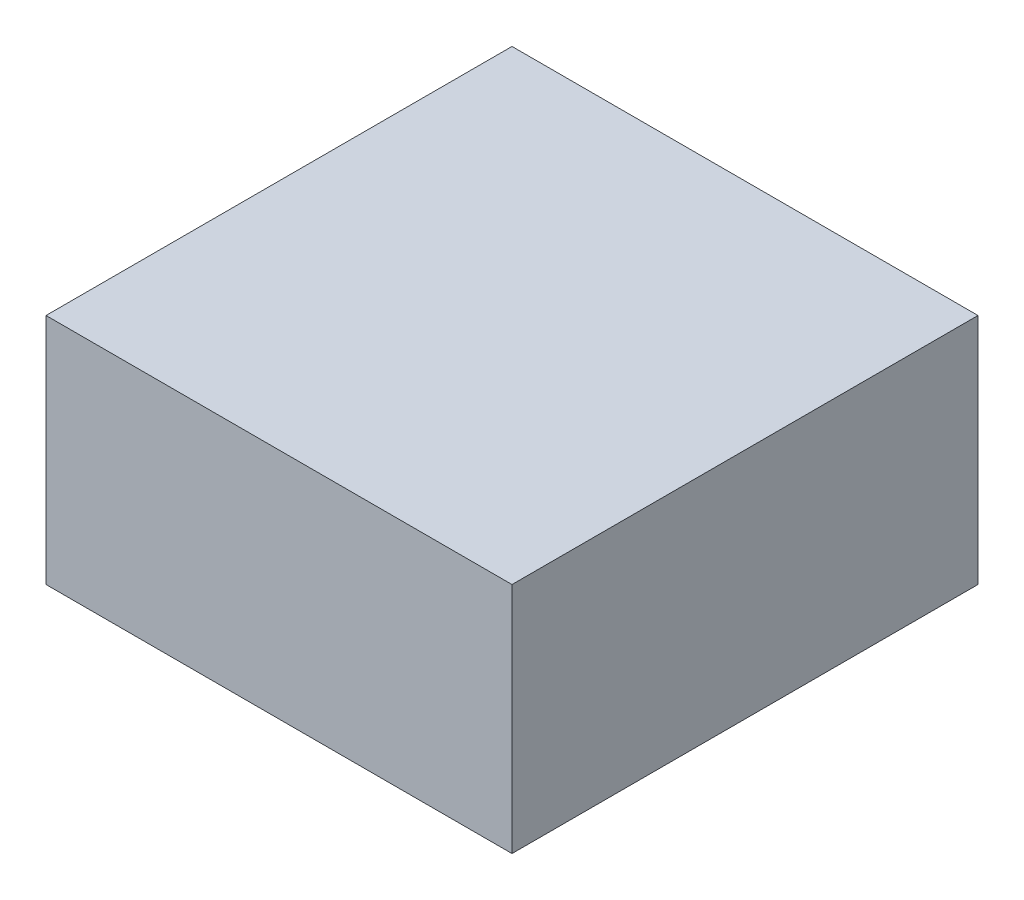
SolidWorks part; units mm, degrees
ref_plane "Front Plane" through (0, 0, 0) normal (0, 0, 1) x (1, 0, 0)
ref_plane "Top Plane" through (0, 0, 0) normal (0, 1, 0) x (1, 0, 0)
ref_plane "Right Plane" through (0, 0, 0) normal (1, 0, 0) x (0, 0, -1)
sketch "Sketch1" plane through (0, 0, 0) normal (0, 1, 0) x (1, 0, 0)
  line L1 (0, 0) -> (18, 0)
  line L2 (0, 0) -> (0, 18)
  line L3 (0, 18) -> (18, 18)
  line L4 (18, 0) -> (18, 18)
  dimension "D1" = 18
extrude "Boss-Extrude1" add sketch "Sketch1" along normal blind 9
